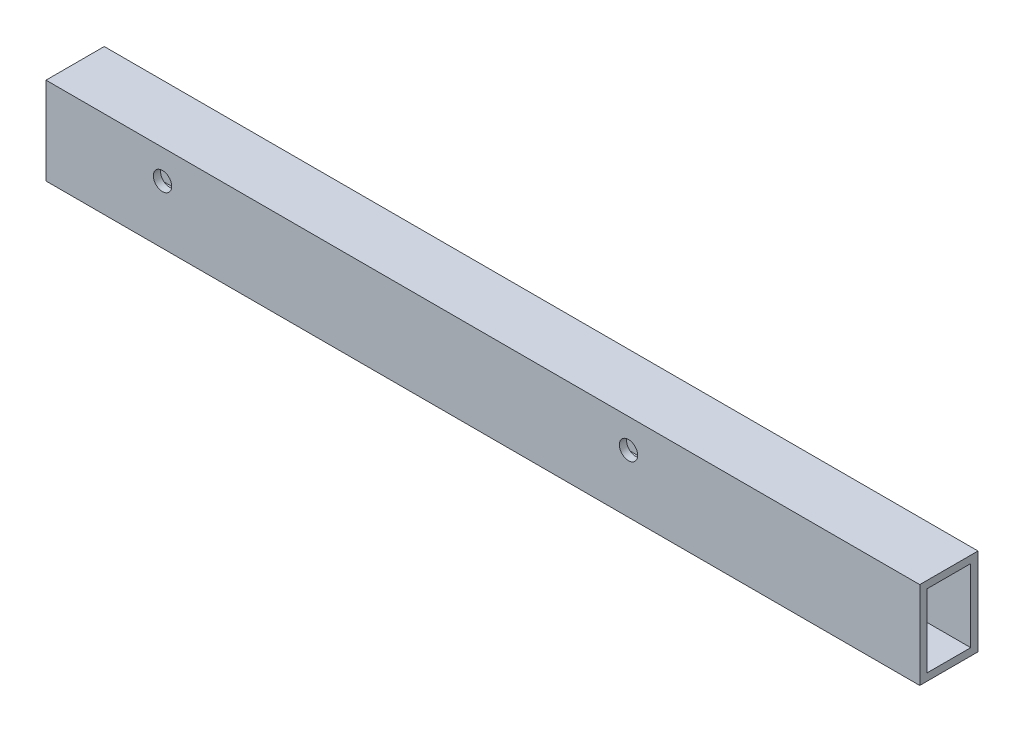
SolidWorks part; units mm, degrees
ref_plane "Front Plane" through (0, 0, 0) normal (0, 0, 1) x (1, 0, 0)
ref_plane "Top Plane" through (0, 0, 0) normal (0, 1, 0) x (1, 0, 0)
ref_plane "Right Plane" through (0, 0, 0) normal (1, 0, 0) x (0, 0, -1)
sketch "Sketch1" plane through (0, 0, 0) normal (1, 0, 0) x (0, 0, -1)
  line L0 (-9.525, -15.875) -> (-9.525, 15.875)
  line L1 (-12.7, -19.05) -> (12.7, -19.05)
  line L2 (-12.7, -19.05) -> (-12.7, 19.05)
  line L3 (-12.7, 19.05) -> (12.7, 19.05)
  line L4 (12.7, -19.05) -> (12.7, 19.05)
  line L5 (-12.7, -19.05) -> (12.7, 19.05) construction
  line L6 (-12.7, 19.05) -> (12.7, -19.05) construction
  line L7 (-9.525, 15.875) -> (9.525, 15.875)
  line L8 (9.525, -15.875) -> (9.525, 15.875)
  line L9 (-9.525, -15.875) -> (9.525, -15.875)
  point P0 (0, 0)
  dimension "D1" = 25.4
  dimension "D2" = 38.1
  dimension "D3" = 3.175
extrude "Boss-Extrude1" add sketch "Sketch1" along normal blind 381
sketch "Sketch2" plane through (0, 0, -12.7) normal (0, 0, -1) x (-1, 0, 0)
  line L0 (-381, 19.05) -> (0, 19.05) construction
  line L1 (0, -19.05) -> (0, 19.05) construction
  line L2 (-50.8, 6.35) -> (-254, 6.35) construction
  circle A0 centre (-50.8, 6.35) radius 4
  circle A1 centre (-254, 6.35) radius 4
  dimension "D1" = 8
  dimension "D2" = 12.7
  dimension "D3" = 50.8
  dimension "D4" = 203.2
extrude "Cut-Extrude1" cut sketch "Sketch2" against normal through all
